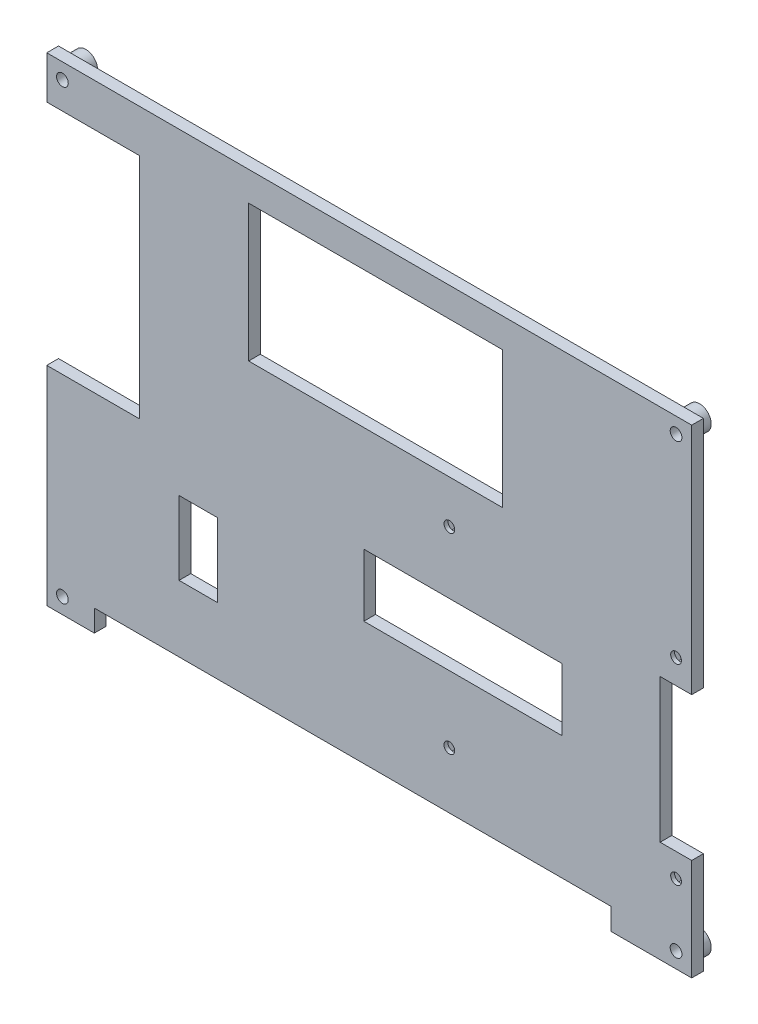
SolidWorks part; units mm, degrees
ref_plane "Alzado" through (0, 0, 0) normal (0, 0, 1) x (1, 0, 0)
ref_plane "Planta" through (0, 0, 0) normal (0, 1, 0) x (1, 0, 0)
ref_plane "Vista lateral" through (0, 0, 0) normal (1, 0, 0) x (0, 0, -1)
sketch "Croquis9" plane through (0, -39.7112, 0) normal (0, 0, 1) x (-1, 0, 0)
  line L0 (0, -57.4941) -> (0, -21.9283) construction
  line L1 (-78.5, 17.5388) -> (78.5, 17.5388) construction
  line L2 (-78.5, 17.5388) -> (-78.5, -96.9612) construction
  line L3 (-78.5, -96.9612) -> (78.5, -96.9612) construction
  line L4 (78.5, 17.5388) -> (78.5, -96.9612) construction
  line L5 (-78.5, 17.5388) -> (78.5, -96.9612) construction
  line L6 (-78.5, -96.9612) -> (78.5, 17.5388) construction
  line L8 (-82.5, 21.5388) -> (82.5, 21.5388)
  line L9 (-82.5, 21.5388) -> (-82.5, -100.9612)
  line L10 (-82.5, -100.9612) -> (82.5, -100.9612)
  line L11 (82.5, 21.5388) -> (82.5, -100.9612)
  line L12 (-82.5, 21.5388) -> (82.5, -100.9612) construction
  line L13 (-82.5, -100.9612) -> (82.5, 21.5388) construction
  circle A0 centre (-78.5, 17.5388) radius 1.5
  circle A1 centre (78.5, 17.5388) radius 1.5
  circle A2 centre (-78.5, -96.9612) radius 1.5
  circle A3 centre (78.5, -96.9612) radius 1.5
  point P0 (0, -39.7112)
  point P10 (0, -39.7112)
  point P14 (0, -39.7112)
  point P17 (0, -39.7112)
  dimension "D4" = 3
  dimension "D1" = 157
  dimension "D2" = 114.5
  dimension "D3" = 4
  dimension "D5" = 4
extrude "Saliente-Extruir7" add sketch "Croquis9" along normal blind 3
sketch "Croquis10" plane through (0, -39.7112, 0) normal (0, 0, -1) x (1, 0, 0)
  circle A0 centre (-78.5, 18.2888) radius 3
  circle A1 centre (78.5, 18.2888) radius 3
  circle A2 centre (78.5, -97.7112) radius 3
  circle A3 centre (-78.5, -97.7112) radius 3
  circle A4 centre (-78.5, 18.2888) radius 1.5
  circle A5 centre (78.5, 18.2888) radius 1.5
  circle A6 centre (78.5, -97.7112) radius 1.5
  circle A7 centre (-78.5, -97.7112) radius 1.5
  dimension "D1" = 6
extrude "Saliente-Extruir4" add sketch "Croquis10" along normal blind 3
sketch "Croquis13" plane through (0, -58.6525, 3) normal (0, 0, -1) x (1, 0, 0)
  line L0 (82.5, 2.5975) -> (82.5, -119.9025) construction
  line L1 (20.5, -17.4025) -> (78.5, -17.4025) construction
  line L2 (20.5, -17.4025) -> (20.5, -66.4025) construction
  line L3 (20.5, -66.4025) -> (78.5, -66.4025) construction
  line L4 (78.5, -17.4025) -> (78.5, -66.4025) construction
  line L5 (20.5, -17.4025) -> (78.5, -66.4025) construction
  line L6 (20.5, -66.4025) -> (78.5, -17.4025) construction
  line L7 (-82.5, 2.5975) -> (82.5, 2.5975) construction
  circle A0 centre (20.5, -17.4025) radius 1.375
  circle A1 centre (78.5, -17.4025) radius 1.375
  circle A2 centre (20.5, -66.4025) radius 1.375
  circle A3 centre (78.5, -66.4025) radius 1.375
  point P15 (49.5, -41.9025)
  dimension "D1" = 2.75
  dimension "D2" = 49
  dimension "D3" = 58
  dimension "D4" = 4
  dimension "D5" = 20
extrude "Cortar-Extruir6" cut sketch "Croquis13" along normal through all
sketch "Croquis15" plane through (0, -0.9962, 3) normal (0, 0, -1) x (-1, 0, 0)
  circle A0 centre (-78.5, -40.2538) radius 3
  circle A1 centre (-20.5, -40.2538) radius 3
  circle A2 centre (-20.5, 8.7462) radius 3
  circle A3 centre (-78.5, 8.7462) radius 3
  circle A8 centre (-78.5, -40.2538) radius 1.375
  circle A9 centre (-20.5, -40.2538) radius 1.375
  circle A10 centre (-20.5, 8.7462) radius 1.375
  circle A11 centre (-78.5, 8.7462) radius 1.375
  dimension "D1" = 6
extrude "Saliente-Extruir5" [suppressed] add sketch "Croquis15" against normal blind 3
sketch "Croquis17" plane through (0, -39.7112, 0) normal (0, 0, -1) x (1, 0, 0)
  line L1 (23.3406, 1.5388) -> (21.9203, 3.9988)
  line L2 (21.9203, 3.9988) -> (19.0797, 3.9988)
  line L3 (19.0797, 3.9988) -> (17.6594, 1.5388)
  line L4 (17.6594, 1.5388) -> (19.0797, -0.9212)
  line L5 (19.0797, -0.9212) -> (21.9203, -0.9212)
  line L6 (21.9203, -0.9212) -> (23.3406, 1.5388)
  line L7 (81.3406, 1.5388) -> (79.9203, 3.9988)
  line L8 (79.9203, 3.9988) -> (77.0797, 3.9988)
  line L9 (77.0797, 3.9988) -> (75.6594, 1.5388)
  line L10 (75.6594, 1.5388) -> (77.0797, -0.9212)
  line L11 (77.0797, -0.9212) -> (79.9203, -0.9212)
  line L12 (79.9203, -0.9212) -> (81.3406, 1.5388)
  line L13 (81.3406, -47.4612) -> (79.9203, -45.0012)
  line L14 (79.9203, -45.0012) -> (77.0797, -45.0012)
  line L15 (77.0797, -45.0012) -> (75.6594, -47.4612)
  line L16 (75.6594, -47.4612) -> (77.0797, -49.9212)
  line L17 (77.0797, -49.9212) -> (79.9203, -49.9212)
  line L18 (79.9203, -49.9212) -> (81.3406, -47.4612)
  line L19 (23.3406, -47.4612) -> (21.9203, -45.0012)
  line L20 (21.9203, -45.0012) -> (19.0797, -45.0012)
  line L21 (19.0797, -45.0012) -> (17.6594, -47.4612)
  line L22 (17.6594, -47.4612) -> (19.0797, -49.9212)
  line L23 (19.0797, -49.9212) -> (21.9203, -49.9212)
  line L24 (21.9203, -49.9212) -> (23.3406, -47.4612)
  circle A0 centre (20.5, 1.5388) radius 2.46 construction
  circle A1 centre (78.5, 1.5388) radius 2.46 construction
  circle A2 centre (78.5, -47.4612) radius 2.46 construction
  circle A3 centre (20.5, -47.4612) radius 2.46 construction
  dimension "D1" = 4.92
extrude "Cortar-Extruir9" cut sketch "Croquis17" against normal blind 2
sketch "Croquis19" plane through (0, 0, 3) normal (0, 0, 1) x (1, 0, 0)
  line L0 (-82.5, 61.25) -> (-82.5, -61.25) construction
  line L1 (-82.5, 50.3205) -> (-58.7483, 50.3205)
  line L2 (-82.5, 50.3205) -> (-82.5, -8.0025)
  line L3 (-82.5, -8.0025) -> (-58.7483, -8.0025)
  line L4 (-58.7483, 50.3205) -> (-58.7483, -8.0025)
  line L5 (-82.5, 50.3205) -> (-58.7483, -8.0025) construction
  line L6 (-82.5, -8.0025) -> (-58.7483, 50.3205) construction
  point P4 (-70.6241, 21.159)
extrude "Cortar-Extruir11" cut sketch "Croquis19" against normal through all
sketch "Croquis20" plane through (0, 0, 3) normal (0, 0, 1) x (1, 0, 0)
  line L0 (82.5, -61.25) -> (82.5, 61.25) construction
  line L1 (82.5, 1.5143) -> (74.4252, 1.5143)
  line L2 (82.5, 1.5143) -> (82.5, -35.2025)
  line L3 (82.5, -35.2025) -> (74.4252, -35.2025)
  line L4 (74.4252, 1.5143) -> (74.4252, -35.2025)
  line L5 (82.5, 1.5143) -> (74.4252, -35.2025) construction
  line L6 (82.5, -35.2025) -> (74.4252, 1.5143) construction
  point P4 (78.4626, -16.8441)
extrude "Cortar-Extruir12" cut sketch "Croquis20" against normal through all
sketch "Croquis21" plane through (0, 0, 3) normal (0, 0, 1) x (1, 0, 0)
  line L0 (-82.5, -61.25) -> (82.5, -61.25) construction
  line L1 (61.8848, -61.25) -> (-70.3307, -61.25)
  line L2 (61.8848, -61.25) -> (61.8848, -55.6971)
  line L3 (61.8848, -55.6971) -> (-70.3307, -55.6971)
  line L4 (-70.3307, -61.25) -> (-70.3307, -55.6971)
  line L5 (61.8848, -61.25) -> (-70.3307, -55.6971) construction
  line L6 (61.8848, -55.6971) -> (-70.3307, -61.25) construction
  point P4 (-4.223, -58.4736)
extrude "Cortar-Extruir13" cut sketch "Croquis21" against normal through all
sketch "Croquis22" plane through (0, 0, 3) normal (0, 0, 1) x (1, 0, 0)
  line L1 (34.1228, 18.7761) -> (-30.8571, 18.7761)
  line L2 (34.1228, 18.7761) -> (34.1228, 53.7567)
  line L3 (34.1228, 53.7567) -> (-30.8571, 53.7567)
  line L4 (-30.8571, 18.7761) -> (-30.8571, 53.7567)
  line L5 (34.1228, 18.7761) -> (-30.8571, 53.7567) construction
  line L6 (34.1228, 53.7567) -> (-30.8571, 18.7761) construction
  point P4 (1.6328, 36.2664)
extrude "Cortar-Extruir14" cut sketch "Croquis22" against normal blind 10
sketch "Croquis23" plane through (0, 0, 3) normal (0, 0, 1) x (1, 0, 0)
  line L1 (-38.8686, -38.7275) -> (-48.6538, -38.7275)
  line L2 (-38.8686, -38.7275) -> (-38.8686, -19.9157)
  line L3 (-38.8686, -19.9157) -> (-48.6538, -19.9157)
  line L4 (-48.6538, -38.7275) -> (-48.6538, -19.9157)
  line L5 (-38.8686, -38.7275) -> (-48.6538, -19.9157) construction
  line L6 (-38.8686, -19.9157) -> (-48.6538, -38.7275) construction
  point P4 (-43.7612, -29.3216)
extrude "Cortar-Extruir15" cut sketch "Croquis23" against normal through all
sketch "Croquis24" plane through (0, 0, 0) normal (0, 0, -1) x (-1, 0, 0)
  line L1 (1.3852, -24.1466) -> (-49.3394, -24.1466)
  line L2 (1.3852, -24.1466) -> (1.3852, -8.1666)
  line L3 (1.3852, -8.1666) -> (-49.3394, -8.1666)
  line L4 (-49.3394, -24.1466) -> (-49.3394, -8.1666)
  line L5 (1.3852, -24.1466) -> (-49.3394, -8.1666) construction
  line L6 (1.3852, -8.1666) -> (-49.3394, -24.1466) construction
  point P4 (-23.9771, -16.1566)
extrude "Cortar-Extruir16" cut sketch "Croquis24" against normal blind 10
